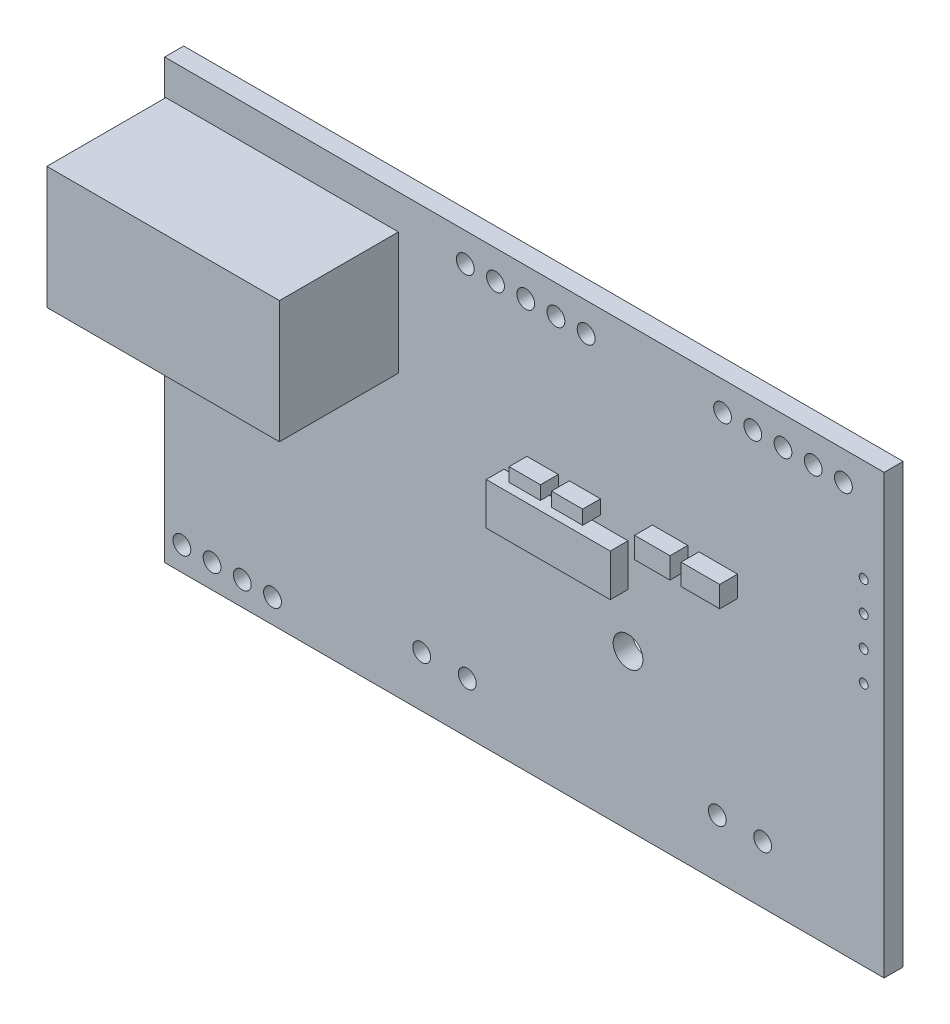
SolidWorks part; units mm, degrees
ref_plane "Plan de face" through (0, 0, 0) normal (0, 0, 1) x (1, 0, 0)
ref_plane "Plan de dessus" through (0, 0, 0) normal (0, 1, 0) x (1, 0, 0)
ref_plane "Plan de droite" through (0, 0, 0) normal (1, 0, 0) x (0, 0, -1)
sketch "Esquisse1" plane through (0, 0, 0) normal (0, 0, 1) x (1, 0, 0)
  line L1 (-30.24, -18.405) -> (30.24, -18.405)
  line L2 (-30.24, -18.405) -> (-30.24, 18.405)
  line L3 (-30.24, 18.405) -> (30.24, 18.405)
  line L4 (30.24, -18.405) -> (30.24, 18.405)
  line L5 (-30.24, -18.405) -> (30.24, 18.405) construction
  line L6 (-30.24, 18.405) -> (30.24, -18.405) construction
  point P0 (0, 0)
  dimension "D1" = 36.81
  dimension "D2" = 60.48
extrude "Boss.-Extru.1" add sketch "Esquisse1" along normal blind 1.6
sketch "Esquisse2" plane through (0, 0, 0) normal (0, 0, -1) x (-1, 0, 0)
  line L0 (195.9209, 394.5463) -> (1101.2543, 394.5463) construction
sketch "holes" plane through (0, 0, 0) normal (0, 0, -1) x (-1, 0, 0)
  line L0 (-19.2001, 15.9712) -> (6.6719, 15.9712) construction
  circle A0 centre (-26.8201, 15.9712) radius 0.7461
  circle A1 centre (-24.2801, 15.9712) radius 0.7461
  circle A2 centre (-21.7401, 15.9712) radius 0.7461
  circle A3 centre (-19.2001, 15.9712) radius 0.7461
  circle A4 centre (-16.6601, 15.9712) radius 0.7461
  circle A5 centre (-0.112, 15.9712) radius 0.75
  circle A6 centre (2.428, 15.9712) radius 0.75
  circle A7 centre (4.968, 15.9712) radius 0.75
  circle A8 centre (-2.652, 15.9712) radius 0.75
  circle A9 centre (-5.192, 15.9712) radius 0.75
  circle A10 centre (-8.7142, -5.3877) radius 1.2504
  circle A11 centre (23.7123, -16.3825) radius 0.75
  circle A12 centre (26.2523, -16.3825) radius 0.75
  circle A13 centre (28.7923, -16.3825) radius 0.75
  circle A14 centre (21.1723, -16.3825) radius 0.75
  circle A15 centre (-16.2197, -13.5656) radius 0.75
  circle A16 centre (-20.0312, -13.5656) radius 0.75
  circle A17 centre (4.7968, -14.1216) radius 0.75
  circle A18 centre (8.6331, -14.1216) radius 0.7493
  dimension "D2" = 3
  dimension "D4" = 3
  dimension "D6" = 1.5
  dimension "D7" = 1.5
  dimension "D1" = 5
  dimension "D3" = 3
  dimension "D5" = 2
extrude "Enlèv. mat.-Extru.1" cut sketch "holes" against normal blind 1.6
sketch "Esquisse4" plane through (0, 0, 1.6) normal (0, 0, 1) x (1, 0, 0)
  circle A0 centre (28.5228, 2.1729) radius 0.375
  circle A1 centre (28.5228, 4.7129) radius 0.375
  circle A2 centre (28.5228, 7.2529) radius 0.375
  circle A3 centre (28.5228, 9.7929) radius 0.375
  dimension "D1" = 4
extrude "Enlèv. mat.-Extru.2" cut sketch "Esquisse4" against normal blind 1.6
sketch "composants" plane through (0, 0, 1.6) normal (0, 0, 1) x (1, 0, 0)
  line L1 (8.7195, 2.6637) -> (-1.7083, 2.6637)
  line L2 (8.7195, 2.6637) -> (8.7195, -0.8732)
  line L3 (8.7195, -0.8732) -> (-1.7083, -0.8732)
  line L4 (-1.7083, 2.6637) -> (-1.7083, -0.8732)
  line L5 (8.7195, 2.6637) -> (-1.7083, -0.8732) construction
  line L6 (8.7195, -0.8732) -> (-1.7083, 2.6637) construction
  line L12 (17.9191, 3.061) -> (14.6753, 3.061)
  line L13 (17.9191, 3.061) -> (17.9191, 4.8374)
  line L14 (17.9191, 4.8374) -> (14.6753, 4.8374)
  line L15 (14.6753, 3.061) -> (14.6753, 4.8374)
  line L16 (13.7389, 3.061) -> (10.7654, 3.061)
  line L17 (13.7389, 3.061) -> (13.7389, 4.8374)
  line L18 (13.7389, 4.8374) -> (10.7654, 4.8374)
  line L19 (10.7654, 3.061) -> (10.7654, 4.8374)
  line L20 (6.4005, 3.3819) -> (3.7771, 3.3819)
  line L21 (6.4005, 3.3819) -> (6.4005, 4.56)
  line L22 (6.4005, 4.56) -> (3.7771, 4.56)
  line L23 (3.7771, 3.3819) -> (3.7771, 4.56)
  line L24 (2.8499, 3.4147) -> (0.2156, 3.4147)
  line L25 (2.8499, 3.4147) -> (2.8499, 4.56)
  line L26 (2.8499, 4.56) -> (0.2156, 4.56)
  line L27 (0.2156, 3.4147) -> (0.2156, 4.56)
  point P0 (3.5056, 0.8952)
extrude "Boss.-Extru.2" add sketch "composants" along normal blind 1.5
sketch "Esquisse6" plane through (0, 0, 1.6) normal (0, 0, 1) x (1, 0, 0)
  line L0 (-30.24, 18.405) -> (-30.24, -18.405) construction
  line L1 (-10.5885, 5.2194) -> (-30.24, 5.2194)
  line L2 (-10.5885, 5.2194) -> (-10.5885, 15.496)
  line L3 (-10.5885, 15.496) -> (-30.24, 15.496)
  line L4 (-30.24, 5.2194) -> (-30.24, 15.496)
extrude "Boss.-Extru.3" add sketch "Esquisse6" along normal blind 10
sketch "Esquisse7" plane through (-30.24, 0, 0) normal (-1, 0, 0) x (0, 0, 1)
  line L1 (1.6, 5.2194) -> (11.6, 5.2194)
  line L2 (1.6, 5.2194) -> (1.6, 15.496)
  line L3 (1.6, 15.496) -> (11.6, 15.496)
  line L4 (11.6, 5.2194) -> (11.6, 15.496)
extrude "Enlèv. mat.-Extru.3" cut sketch "Esquisse7" against normal blind 0.1
